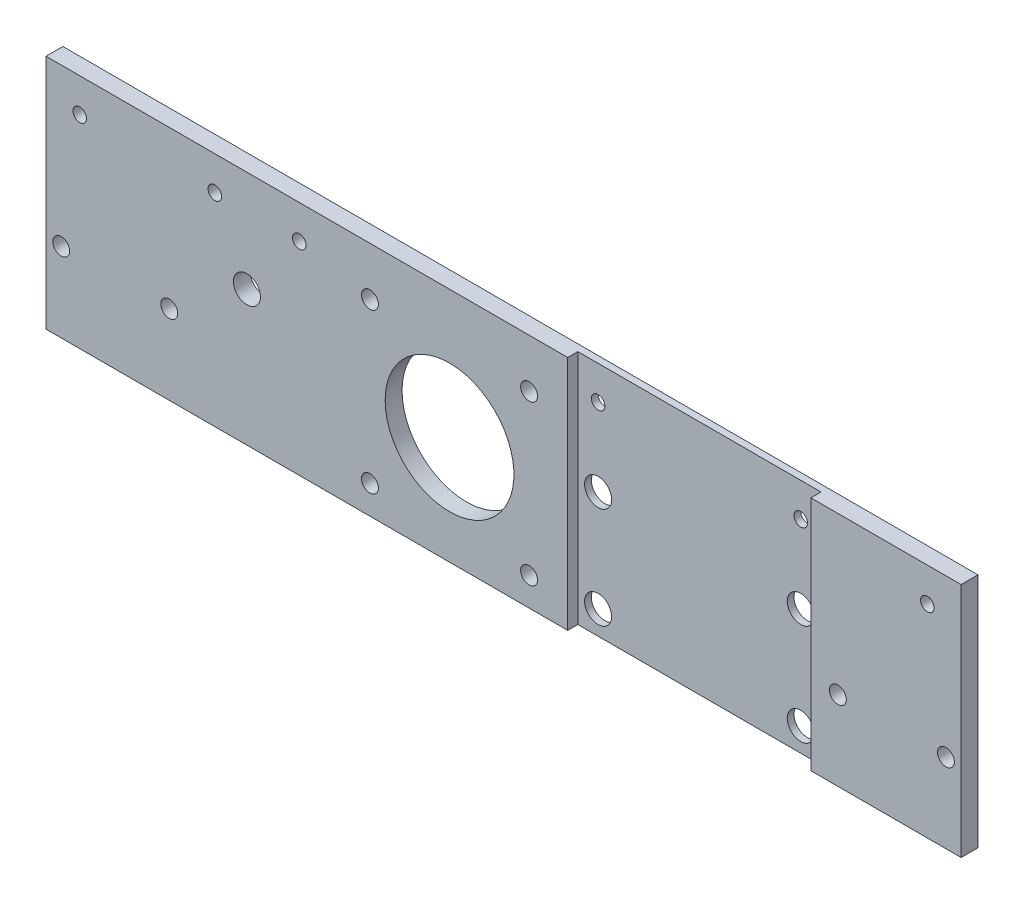
SolidWorks part; units mm, degrees
ref_plane "Ebene vorne" through (0, 0, 0) normal (0, 0, 1) x (1, 0, 0)
ref_plane "Ebene oben" through (0, 0, 0) normal (0, 1, 0) x (1, 0, 0)
ref_plane "Ebene rechts" through (0, 0, 0) normal (1, 0, 0) x (0, 0, -1)
sketch "Skizze1" plane through (0, 0, 0) normal (0, 0, 1) x (1, 0, 0)
  line L1 (0, 0) -> (271, 0)
  line L2 (0, 0) -> (0, 70)
  line L3 (0, 70) -> (271, 70)
  line L4 (271, 0) -> (271, 70)
  dimension "D1" = 271
  dimension "D2" = 70
extrude "Aufsatz-Linear austragen1" add sketch "Skizze1" along normal blind 5
sketch "Skizze2" plane through (0, 0, 5) normal (0, 0, 1) x (1, 0, 0)
  line L0 (271, 70) -> (0, 70) construction
  line L1 (154.5, 70) -> (226.5, 70)
  line L2 (154.5, 70) -> (154.5, 0)
  line L3 (154.5, 0) -> (226.5, 0)
  line L4 (226.5, 70) -> (226.5, 0)
  line L5 (0, 0) -> (271, 0) construction
  line L7 (271, 0) -> (271, 70) construction
  dimension "D1" = 72
  dimension "D2" = 44.5
extrude "Schnitt-Linear austragen1" cut sketch "Skizze2" against normal blind 3
sketch "Skizze3" plane through (0, 0, 0) normal (0, 0, -1) x (-1, 0, 0)
  line L0 (-271, 0) -> (-271, 70) construction
  line L3 (0, 0) -> (-271, 0) construction
  circle A0 centre (-160.5, 37) radius 4
  circle A1 centre (-220.5, 37) radius 4
  circle A2 centre (-220.5, 7) radius 4
  circle A3 centre (-160.5, 7) radius 4
  dimension "D1" = 8
  dimension "D2" = 30
  dimension "D3" = 50.5
  dimension "D4" = 60
  dimension "D5" = 7
extrude "Schnitt-Linear austragen2" cut sketch "Skizze3" against normal blind 10
sketch "Skizze4" plane through (0, 0, 0) normal (0, 0, -1) x (-1, 0, 0)
  line L3 (-271, 0) -> (-271, 70) construction
  line L4 (0, 0) -> (-271, 0) construction
  circle A0 centre (-234.5, 23.5) radius 2.5
  circle A1 centre (-266.5, 23.5) radius 2.5
  dimension "D1" = 5
  dimension "D2" = 4.5
  dimension "D3" = 23.5
  dimension "D4" = 32
extrude "Schnitt-Linear austragen3" cut sketch "Skizze4" against normal blind 10
sketch "Skizze5" plane through (0, 0, 0) normal (0, 0, -1) x (-1, 0, 0)
  line L0 (0, 0) -> (-271, 0) construction
  line L1 (0, 70) -> (0, 0) construction
  circle A0 centre (-36.5, 23.5) radius 2.5
  circle A1 centre (-4.5, 23.5) radius 2.5
  dimension "D4" = 5
  dimension "D1" = 23.5
  dimension "D2" = 4.5
  dimension "D3" = 32
extrude "Schnitt-Linear austragen4" cut sketch "Skizze5" against normal blind 10
sketch "Skizze6" plane through (0, 0, 0) normal (0, 0, -1) x (-1, 0, 0)
  line L0 (0, 70) -> (0, 0) construction
  line L2 (-271, 70) -> (0, 70) construction
  line L3 (-271, 0) -> (-271, 70) construction
  circle A0 centre (-10, 60) radius 2
  circle A1 centre (-50, 60) radius 2
  circle A2 centre (-160.5, 60) radius 2
  circle A3 centre (-220.5, 60) radius 2
  circle A4 centre (-261, 60) radius 2
  dimension "D1" = 4
  dimension "D2" = 10
  dimension "D3" = 10
  dimension "D4" = 50
  dimension "D5" = 10
  dimension "D6" = 50.5
  dimension "D7" = 110.5
extrude "Schnitt-Linear austragen5" cut sketch "Skizze6" against normal blind 10
sketch "Skizze7" plane through (0, 0, 0) normal (0, 0, -1) x (-1, 0, 0)
  line L0 (0, 70) -> (0, 0) construction
  line L1 (0, 0) -> (-271, 0) construction
  circle A0 centre (-119.5, 32) radius 19.0625
  circle A1 centre (-95.93, 8.43) radius 2.5
  circle A2 centre (-143.07, 8.43) radius 2.5
  circle A3 centre (-95.93, 55.57) radius 2.5
  circle A4 centre (-143.07, 55.57) radius 2.5
  dimension "D1" = 5
  dimension "D2" = 38.125
  dimension "D8" = 32
  dimension "D3" = 95.93
  dimension "D4" = 47.14
  dimension "D5" = 47.14
  dimension "D6" = 119.5
  dimension "D7" = 8.43
extrude "Schnitt-Linear austragen6" cut sketch "Skizze7" against normal blind 10
sketch "Skizze8" plane through (0, 0, 0) normal (0, 0, -1) x (-1, 0, 0)
  line L0 (-271, 70) -> (0, 70) construction
  line L1 (0, 70) -> (0, 0) construction
  circle A0 centre (-59.5, 40) radius 4
  dimension "D2" = 8
  dimension "D1" = 30
  dimension "D3" = 59.5
extrude "Schnitt-Linear austragen7" cut sketch "Skizze8" against normal blind 10
sketch "Skizze9" plane through (0, 0, 5) normal (0, 0, 1) x (1, 0, 0)
  line L0 (154.5, 70) -> (0, 70) construction
  line L1 (0, 70) -> (0, 0) construction
  circle A0 centre (75, 60) radius 2
  dimension "D1" = 4
  dimension "D2" = 10
  dimension "D3" = 75
extrude "Schnitt-Linear austragen8" cut sketch "Skizze9" against normal blind 10
